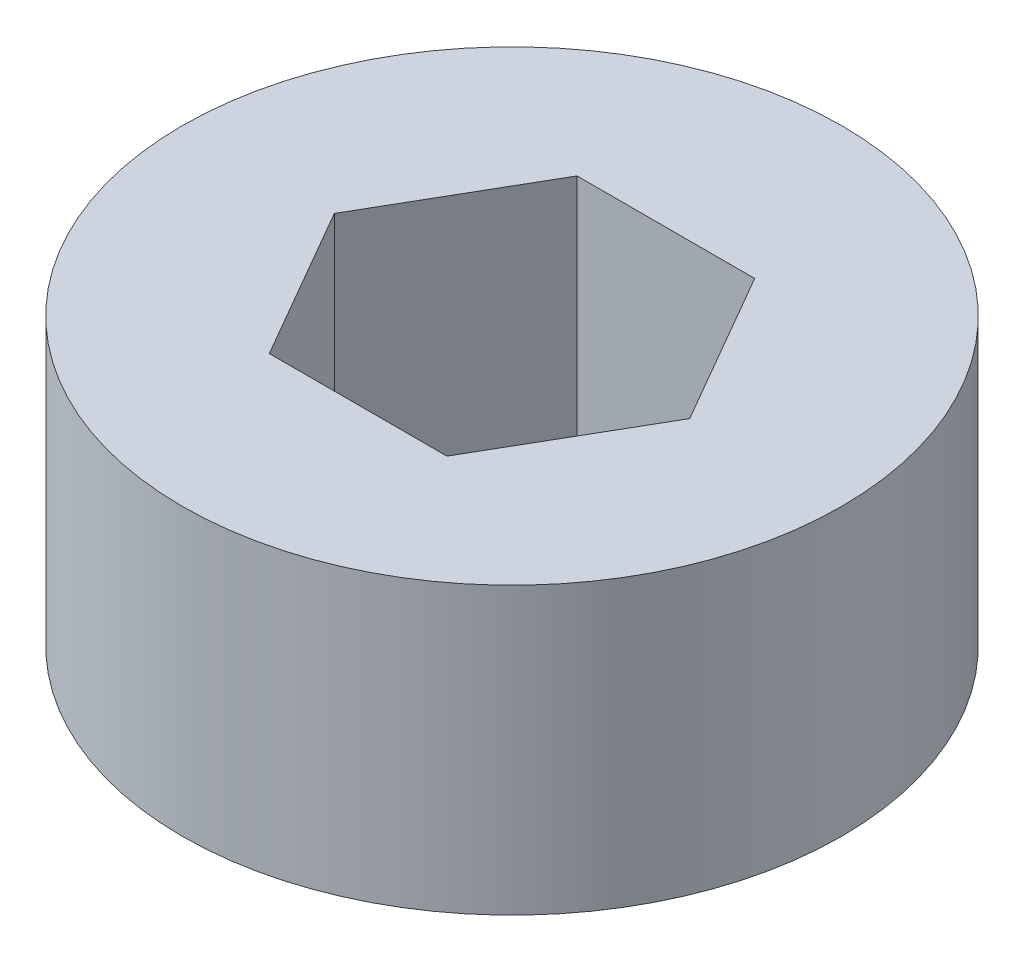
SolidWorks part; units mm, degrees
ref_plane "Front Plane" through (0, 0, 0) normal (0, 0, 1) x (1, 0, 0)
ref_plane "Top Plane" through (0, 0, 0) normal (0, 1, 0) x (1, 0, 0)
ref_plane "Right Plane" through (0, 0, 0) normal (1, 0, 0) x (0, 0, -1)
sketch "Sketch1" plane through (0, 0, 0) normal (0, 1, 0) x (1, 0, 0)
  circle A0 centre (0, 0) radius 15
  dimension "D1" = 30
extrude "Boss-Extrude1" add sketch "Sketch1" along normal blind 13
sketch "Sketch3" plane through (0, 13, 0) normal (0, 1, 0) x (1, 0, 0)
  line L1 (8.0829, 0) -> (4.0415, 7)
  line L2 (4.0415, 7) -> (-4.0415, 7)
  line L3 (-4.0415, 7) -> (-8.0829, 0)
  line L4 (-8.0829, 0) -> (-4.0415, -7)
  line L5 (-4.0415, -7) -> (4.0415, -7)
  line L6 (4.0415, -7) -> (8.0829, 0)
  circle A0 centre (0, 0) radius 7 construction
  dimension "D1" = 14
extrude "Cut-Extrude1" cut sketch "Sketch3" against normal blind 32 and the other way blind 26
equation "\"21.24.00mm\"=10"
